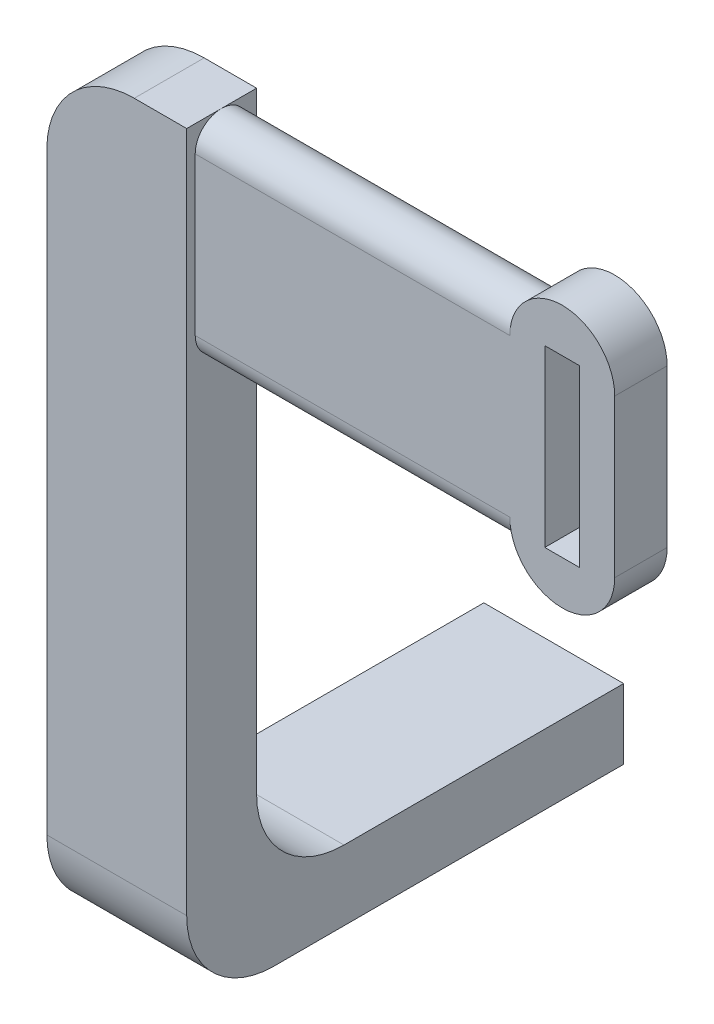
SolidWorks part; units mm, degrees
ref_plane "Front Plane" through (0, 0, 0) normal (0, 0, 1) x (1, 0, 0)
ref_plane "Top Plane" through (0, 0, 0) normal (0, 1, 0) x (1, 0, 0)
ref_plane "Right Plane" through (0, 0, 0) normal (1, 0, 0) x (0, 0, -1)
sketch "Arm Feature Sketch" plane through (0, 0, 0) normal (0, 0, 1) x (1, 0, 0)
  line L1 (-8, 4) -> (8, 4)
  line L2 (-8, 4) -> (-8, -4)
  line L3 (-8, -4) -> (8, -4)
  line L4 (8, 4) -> (8, -4)
  line L5 (-8, 4) -> (8, -4) construction
  line L6 (-8, -4) -> (8, 4) construction
  point P0 (0, 0)
  dimension "D1" = 16
  dimension "D2" = 8
extrude "Arm Feature" add sketch "Arm Feature Sketch" along normal blind 50 contours L1 L4 L3 L2
sketch "Tab Feature Sketch" plane through (0, -4, 0) normal (0, 1, 0) x (1, 0, 0)
  line L0 (-4, 0) -> (4, 0)
  line L1 (-4, 0) -> (-4, -25)
  line L2 (4, 0) -> (4, -25)
  line L3 (-4, -25) -> (4, -25)
  line L4 (-8, 0) -> (8, 0) construction
  dimension "D1" = 25
extrude "Tab Feature" cut sketch "Tab Feature Sketch" along normal blind 5
sketch "Leg Feature Sketch" plane through (0, 4, 0) normal (0, 1, 0) x (1, 0, 0)
  line L0 (-8, -50) -> (8, -50)
  line L1 (-8, -50) -> (-8, -42)
  line L2 (8, -50) -> (8, -42)
  line L3 (-8, -42) -> (8, -42)
  dimension "D1" = 8
extrude "Leg Feature" add sketch "Leg Feature Sketch" along normal blind 80
sketch "Slot Feature Sketch" plane through (8, 0, 0) normal (1, 0, 0) x (0, 0, -1)
  line L0 (-46.0252, 81) -> (-46.0252, 63) construction
  line L1 (-43.0252, 81) -> (-43.0252, 63)
  line L2 (-49.0252, 81) -> (-49.0252, 63)
  line L3 (-50, 84) -> (-42, 84) construction
  arc A0 (-43.0252, 81) -> (-49.0252, 81) centre (-46.0252, 81) ccw
  arc A1 (-49.0252, 63) -> (-43.0252, 63) centre (-46.0252, 63) ccw
  point P2 (-46.0252, 72)
  dimension "D1" = 12
  dimension "D2" = 6
  dimension "D3" = 18
extrude "Slot Feature" add sketch "Slot Feature Sketch" along normal blind 42
sketch "Strap Feature Sketch" plane through (0, 0, 43.0252) normal (0, 0, -1) x (-1, 0, 0)
  line L0 (-50, 63) -> (-50, 81) construction
  line L1 (-50, 63) -> (-50, 81) construction
  line L2 (-56, 63) -> (-56, 81)
  line L3 (-44, 63) -> (-44, 81)
  arc A0 (-56, 63) -> (-44, 63) centre (-50, 63) ccw
  arc A1 (-44, 81) -> (-56, 81) centre (-50, 81) ccw
  point P5 (-50, 72)
extrude "Strap Feature" add sketch "Strap Feature Sketch" against normal blind 6
sketch "Strap Cut Sketch" plane through (0, 0, 49.0252) normal (0, 0, 1) x (1, 0, 0)
  line L1 (48, 82) -> (52, 82)
  line L2 (48, 82) -> (48, 62)
  line L3 (48, 62) -> (52, 62)
  line L4 (52, 82) -> (52, 62)
  line L5 (48, 82) -> (52, 62) construction
  line L6 (48, 62) -> (52, 82) construction
  point P0 (50, 72)
  dimension "D1" = 20
  dimension "D2" = 4
extrude "Strap Cut" cut sketch "Strap Cut Sketch" against normal blind 6 contours L2 L3 L4 L1
fillet "Fillet1" radius 10 1 edges at (0, -4, 50)
fillet "Fillet2" radius 10 1 edges at (0, 4, 42)
fillet "Fillet3" radius 10 1 edges at (-8, 84, 46)
